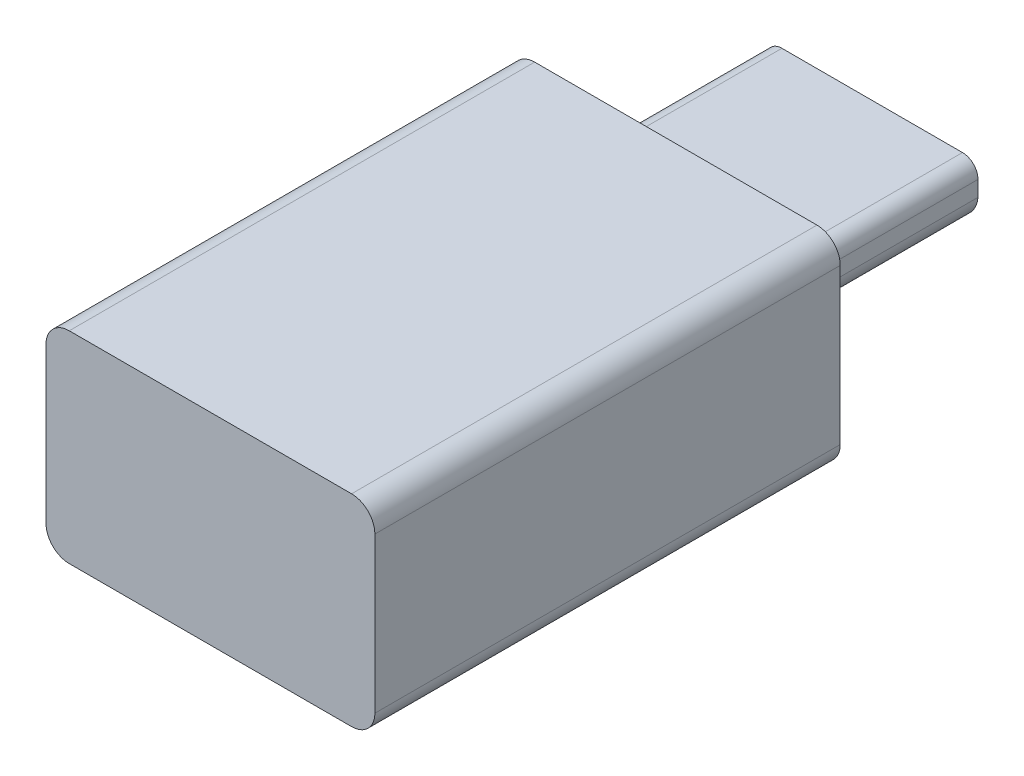
SolidWorks part; units mm, degrees
ref_plane "Front Plane" through (0, 0, 0) normal (0, 0, 1) x (1, 0, 0)
ref_plane "Top Plane" through (0, 0, 0) normal (0, 1, 0) x (1, 0, 0)
ref_plane "Right Plane" through (0, 0, 0) normal (1, 0, 0) x (0, 0, -1)
sketch "Sketch1" plane through (0, 0, 87.6019) normal (0, 0, -1) x (-1, 0, 0)
  line L1 (38.2707, 36.8406) -> (47.3707, 36.8406)
  line L2 (37.5207, 36.0906) -> (37.5207, 31.0906)
  line L3 (38.2707, 30.3406) -> (47.3707, 30.3406)
  line L4 (48.1207, 36.0906) -> (48.1207, 31.0906)
  arc A0 (37.5207, 31.0906) -> (38.2707, 30.3406) centre (38.2707, 31.0906) ccw
  arc A1 (47.3707, 30.3406) -> (48.1207, 31.0906) centre (47.3707, 31.0906) ccw
  arc A2 (47.3707, 36.8406) -> (48.1207, 36.0906) centre (47.3707, 36.0906) cw
  arc A3 (38.2707, 36.8406) -> (37.5207, 36.0906) centre (38.2707, 36.0906) ccw
  point P8 (48.1207, 30.3406)
  point P11 (48.1207, 36.8406)
  point P14 (37.5207, 36.8406)
  dimension "D3" = 0.75
  dimension "D1" = 10.6
  dimension "D2" = 6.5
extrude "Boss-Extrude1" add sketch "Sketch1" along normal blind 15
sketch "Sketch2" plane through (0, 0, 72.6019) normal (0, 0, -1) x (-1, 0, 0)
  line L0 (42.8207, 36.8406) -> (42.8207, 28.6005) construction
  line L1 (47.3707, 36.8406) -> (38.2707, 36.8406) construction
  line L2 (37.5207, 33.5906) -> (48.1207, 33.5906) construction
  line L3 (37.5207, 36.0906) -> (37.5207, 31.0906) construction
  line L4 (48.1207, 31.0906) -> (48.1207, 36.0906) construction
  line L5 (40.3207, 33.0506) -> (45.3207, 33.0506)
  line L6 (39.9107, 34.8806) -> (45.7307, 34.8806)
  line L7 (46.2307, 34.3806) -> (46.2307, 33.8806)
  line L8 (40.3207, 33.0506) -> (45.3207, 33.0506)
  line L9 (39.4107, 34.3806) -> (39.4107, 33.8806)
  arc A0 (45.3207, 33.0506) -> (46.2307, 33.8806) centre (45.3207, 33.9644) ccw
  arc A1 (45.7307, 34.8806) -> (46.2307, 34.3806) centre (45.7307, 34.3806) cw
  arc A2 (39.9107, 34.8806) -> (39.4107, 34.3806) centre (39.9107, 34.3806) ccw
  arc A3 (40.3207, 33.0506) -> (39.4107, 33.8806) centre (40.3207, 33.9644) cw
  point P10 (42.8207, 33.5906)
  point P13 (42.8207, 33.0506)
  point P15 (39.4107, 34.8806)
  point P19 (46.2307, 34.8806)
  point P26 (42.8207, 34.8806)
  dimension "D2" = 0.5
  dimension "D1" = 1
  dimension "D3" = 2.5
  dimension "D4" = 3.79
extrude "Boss-Extrude2" add sketch "Sketch2" along normal blind 6.33 contours A3 L5 A0 L7 A1 L6 A2 L9
ref_plane "Plane1" through (-42.8207, 0, 0) normal (1, 0, 0) x (0, 0, -1)
